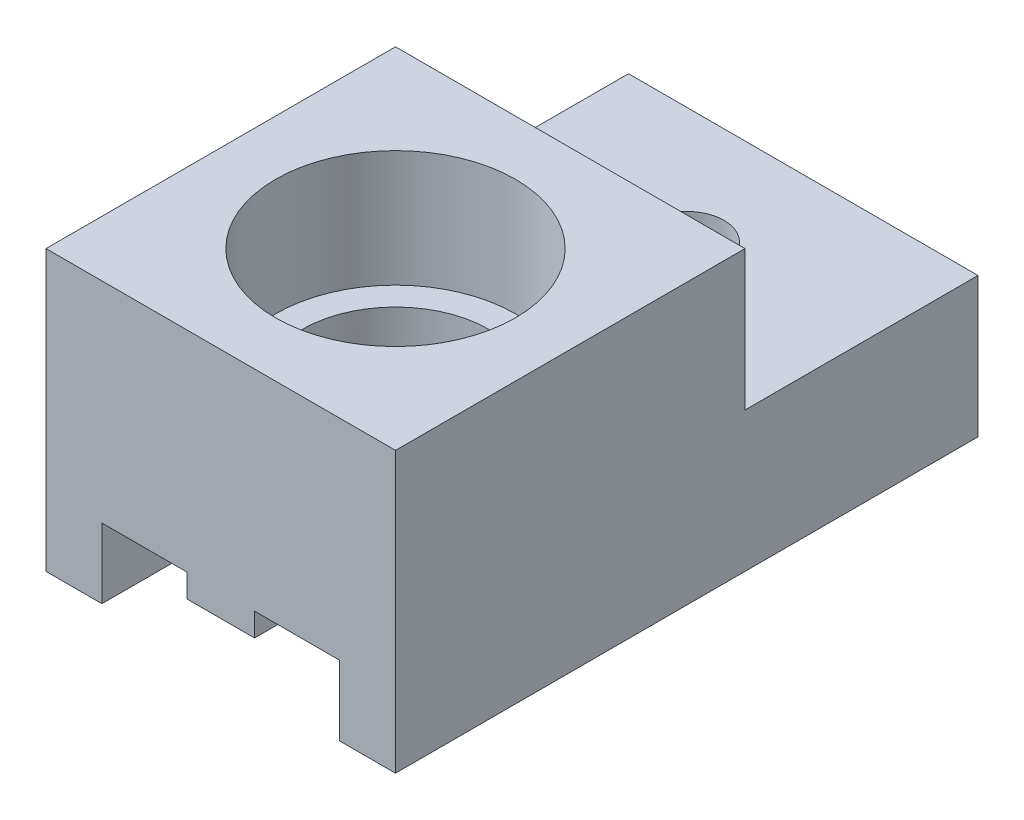
SolidWorks part; units mm, degrees
ref_plane "Front Plane" through (0, 0, 0) normal (0, 0, 1) x (1, 0, 0)
ref_plane "Top Plane" through (0, 0, 0) normal (0, 1, 0) x (1, 0, 0)
ref_plane "Right Plane" through (0, 0, 0) normal (1, 0, 0) x (0, 0, -1)
sketch "Sketch1" plane through (0, 0, 0) normal (0, 0, 1) x (1, 0, 0)
  line L0 (-5.1, 0) -> (-5.1, -3)
  line L1 (-5.1, 0) -> (-1.45, 0)
  line L2 (-1.45, 0) -> (-1.45, -1)
  line L3 (-1.45, -1) -> (1.45, -1)
  line L4 (1.45, -1) -> (1.45, 0)
  line L5 (1.45, 0) -> (5.1, 0)
  line L6 (5.1, 0) -> (5.1, -3)
  line L7 (7.5, 9) -> (-7.5, 9)
  line L8 (-5.1, -3) -> (-7.5, -3)
  line L9 (-7.5, -3) -> (-7.5, 9)
  line L10 (5.1, -3) -> (7.5, -3)
  line L11 (7.5, -3) -> (7.5, 9)
  point P0 (0, -1)
  point P9 (8.4296, 7)
  dimension "D1" = 2.9
  dimension "D2" = 10.2
  dimension "D3" = 1
  dimension "D4" = 3
  dimension "D5" = 12
  dimension "D6" = 15
extrude "Main" add sketch "Sketch1" along normal blind 25
sketch "Sketch2" plane through (0, 9, 0) normal (0, 1, 0) x (1, 0, 0)
  line L0 (7.5, -25) -> (-7.5, -25) construction
  circle A0 centre (0, -17.5) radius 5.15
  dimension "D1" = 10.3
  dimension "D2" = 7.5
extrude "RollingHole" cut sketch "Sketch2" against normal blind 5
sketch "Sketch3" plane through (0, 4, 0) normal (0, 1, 0) x (1, 0, 0)
  circle A0 centre (0, -17.5) radius 4
  circle A2 centre (0, -17.5) radius 5.15 construction
  dimension "D1" = 8
extrude "Cut-Extrude2" cut sketch "Sketch3" against normal through all
sketch "Sketch4" plane through (0, 9, 0) normal (0, 1, 0) x (1, 0, 0)
  circle A0 centre (0, -5) radius 1.6
  dimension "D1" = 3.2
  dimension "D2" = 5
extrude "FixHole" cut sketch "Sketch4" against normal through all
sketch "Sketch5" plane through (-7.5, 0, 0) normal (-1, 0, 0) x (0, 0, 1)
  line L1 (0, 9) -> (10, 9)
  line L2 (0, 9) -> (0, 3)
  line L3 (0, 3) -> (10, 3)
  line L4 (10, 9) -> (10, 3)
  dimension "D1" = 3
  dimension "D2" = 10
extrude "Cut-Extrude4" cut sketch "Sketch5" against normal through all
